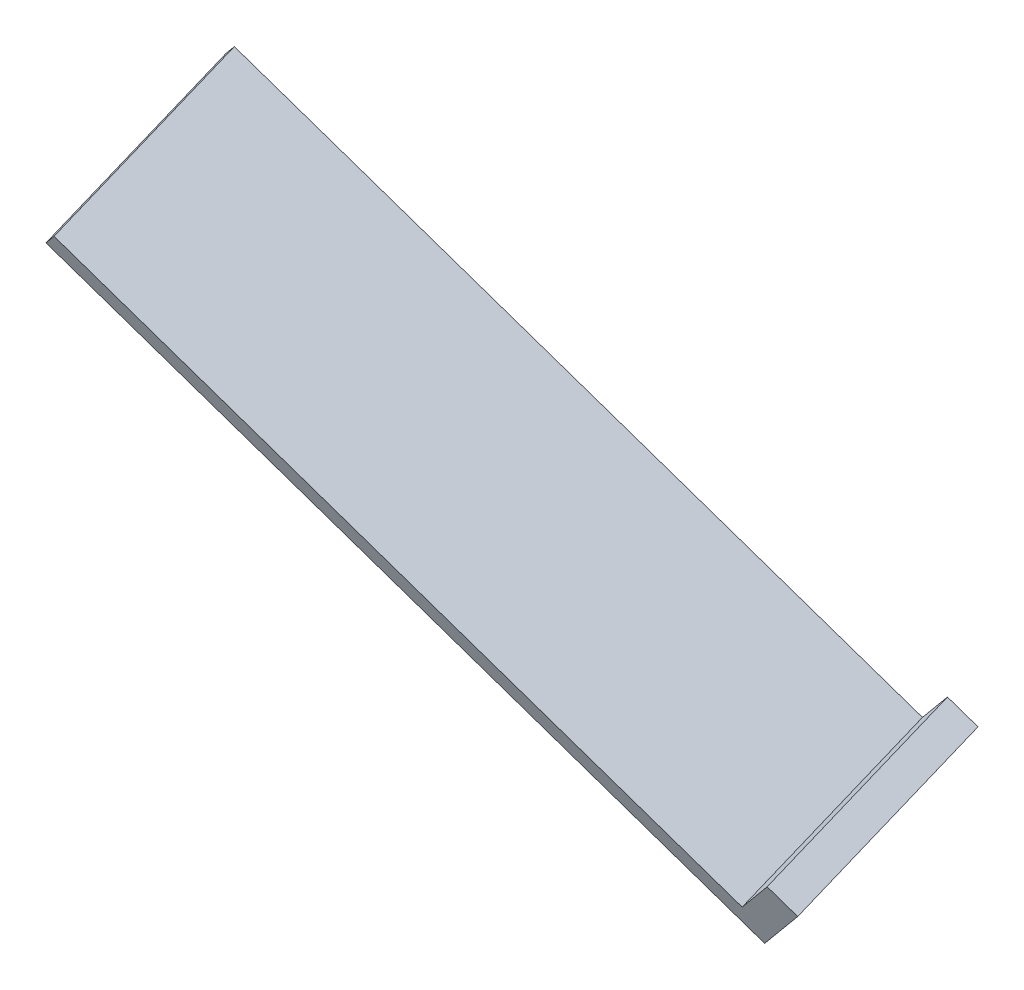
SolidWorks part; units mm, degrees
ref_plane "Front Plane" through (0, 0, 0) normal (0, 0, 1) x (1, 0, 0)
ref_plane "Top Plane" through (0, 0, 0) normal (0, 1, 0) x (1, 0, 0)
ref_plane "Right Plane" through (0, 0, 0) normal (1, 0, 0) x (0, 0, -1)
ref_plane "Plano1" through (-33.8802, -37.6278, -15.4801) normal (-0.6399, -0.7107, -0.2924) x (-0.7685, 0.5918, 0.2435)
sketch "Croquis3" plane through (-33.8802, -37.6278, -15.4801) normal (-0.6399, -0.7107, -0.2924) x (-0.7685, 0.5918, 0.2435)
  line L0 (-24.3873, -104.9876) -> (-25.6886, -104.9876) construction
  line L1 (-25.6886, -104.9876) -> (-53.6886, -104.9876) construction
  line L2 (-24.3873, -96.5876) -> (-24.3873, -104.9876) construction
  line L3 (-25.6886, -96.5876) -> (-24.3873, -96.5876) construction
  line L4 (-53.6886, -96.5876) -> (-25.6886, -96.5876) construction
  line L5 (-53.6886, -104.9876) -> (-53.6886, -96.5876) construction
  line L6 (-24.3873, -104.9876) -> (-25.6886, -104.9876)
  line L7 (-25.6886, -104.9876) -> (-53.6886, -104.9876)
  line L8 (-24.3873, -96.5876) -> (-24.3873, -104.9876)
  line L9 (-25.6886, -96.5876) -> (-24.3873, -96.5876)
  line L10 (-53.6886, -96.5876) -> (-25.6886, -96.5876)
  line L11 (-53.6886, -104.9876) -> (-53.6886, -96.5876)
extrude "Saliente-Extruir1" add sketch "Croquis3" along normal blind 1 from offset 3.1
sketch "Croquis4" plane through (-35.8639, -39.8309, -16.3865) normal (0.6399, 0.7107, 0.2924) x (0.7685, -0.5918, -0.2435)
  line L0 (24.3873, -104.9876) -> (65.3782, -104.9876) construction
  line L1 (24.3873, -104.9876) -> (25.6886, -104.9876)
  line L2 (24.3873, -104.9876) -> (24.3873, -96.5876)
  line L3 (24.3873, -96.5876) -> (25.6886, -96.5876)
  line L4 (25.6886, -104.9876) -> (25.6886, -96.5876)
  line L5 (53.6886, -96.5876) -> (54.9899, -96.5876)
  line L6 (53.6886, -96.5876) -> (53.6886, -104.9876)
  line L7 (53.6886, -104.9876) -> (54.9899, -104.9876)
  line L8 (54.9899, -96.5876) -> (54.9899, -104.9876)
  line M6 (53.6886, -104.9876) -> (53.6886, -96.5876)
extrude "Saliente-Extruir2" add sketch "Croquis4" along normal up to surface and the other way up to surface contours L8 L5 L7 M6
sketch "Croquis5" plane through (-33.8802, -37.6278, -15.4801) normal (-0.6399, -0.7107, -0.2924) x (-0.7685, 0.5918, 0.2435)
  point P0 (0, 0)
